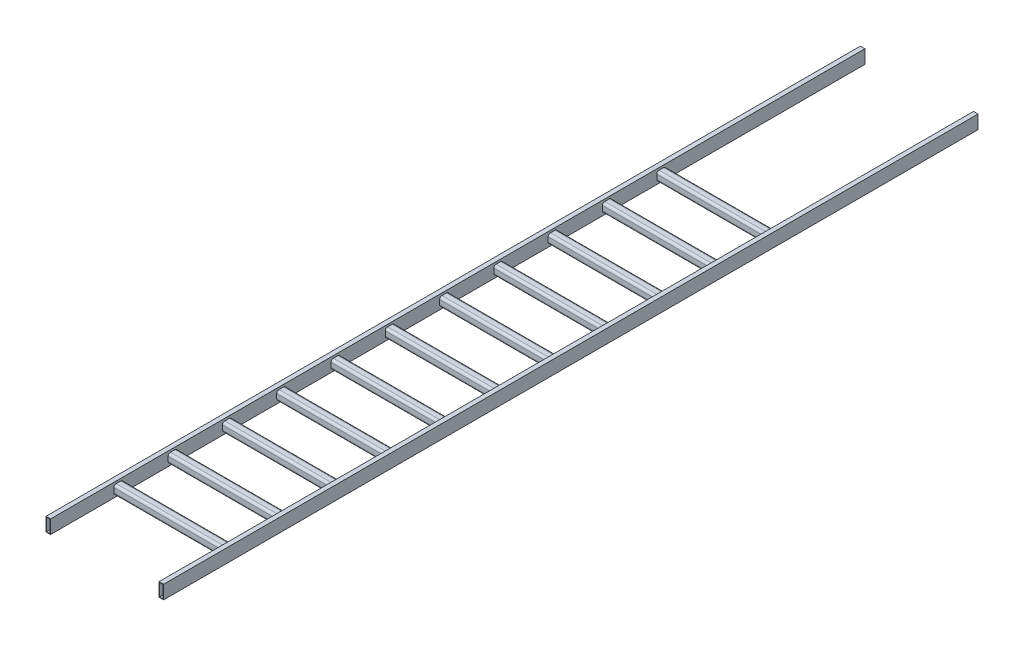
SolidWorks part; units mm, degrees
other "DetailItem3"
ref_plane "Front Plane" through (0, 0, 0) normal (0, 0, 1) x (1, 0, 0)
ref_plane "Top Plane" through (0, 0, 0) normal (0, 1, 0) x (1, 0, 0)
ref_plane "Right Plane" through (0, 0, 0) normal (1, 0, 0) x (0, 0, -1)
sketch "Sketch15" plane through (0, 0, 0) normal (0, 0, 1) x (1, 0, 0)
  line L0 (0, 222.2231) -> (0, -267.675) construction
  line L1 (-483.3871, 0) -> (603.0676, 0) construction
  line L2 (307.975, 34.925) -> (327.025, -34.925) construction
  line L3 (-304.8, -38.1) -> (-330.2, -38.1)
  line L4 (-304.8, -38.1) -> (-304.8, 38.1)
  line L5 (-304.8, 38.1) -> (-330.2, 38.1)
  line L6 (-330.2, -38.1) -> (-330.2, 38.1)
  line L7 (-304.8, -38.1) -> (-330.2, 38.1) construction
  line L8 (-304.8, 38.1) -> (-330.2, -38.1) construction
  line L9 (-307.975, -34.925) -> (-327.025, -34.925)
  line L10 (-307.975, -34.925) -> (-307.975, 34.925)
  line L11 (-307.975, 34.925) -> (-327.025, 34.925)
  line L12 (-327.025, -34.925) -> (-327.025, 34.925)
  line L13 (-307.975, -34.925) -> (-327.025, 34.925) construction
  line L14 (-307.975, 34.925) -> (-327.025, -34.925) construction
  line L15 (307.975, -34.925) -> (327.025, 34.925) construction
  line L16 (304.8, 38.1) -> (330.2, -38.1) construction
  line L17 (304.8, -38.1) -> (330.2, 38.1) construction
  line L18 (327.025, -34.925) -> (327.025, 34.925)
  line L19 (307.975, 34.925) -> (327.025, 34.925)
  line L20 (307.975, -34.925) -> (307.975, 34.925)
  line L21 (307.975, -34.925) -> (327.025, -34.925)
  line L22 (330.2, -38.1) -> (330.2, 38.1)
  line L23 (304.8, 38.1) -> (330.2, 38.1)
  line L24 (304.8, -38.1) -> (304.8, 38.1)
  line L25 (304.8, -38.1) -> (330.2, -38.1)
  point P3 (-317.5, 0)
  point P10 (-317.5, 0)
  point P24 (317.5, 0)
  dimension "D1" = 25.4
  dimension "D2" = 76.2
  dimension "D3" = 3.175
  dimension "D4" = 3.175
  dimension "D5" = 660.4
extrude "Boss-Extrude1" add sketch "Sketch15" along normal blind 4572
sketch "Sketch17" plane through (0, 0, 0) normal (0, 1, 0) x (1, 0, 0)
  line L0 (-304.8, -1143) -> (304.8, -1143)
  line L1 (-304.8, -4572) -> (-304.8, 0) construction
  line L2 (304.8, -4572) -> (304.8, 0) construction
  line L3 (330.2, 0) -> (304.8, 0) construction
  line L4 (-304.8, -1447.8) -> (304.8, -1447.8)
  line L5 (-304.8, -1752.6) -> (304.8, -1752.6)
  line L6 (-304.8, -2057.4) -> (304.8, -2057.4)
  line L7 (-304.8, -2362.2) -> (304.8, -2362.2)
  line L8 (-304.8, -2667) -> (304.8, -2667)
  line L9 (-304.8, -2971.8) -> (304.8, -2971.8)
  line L10 (-304.8, -3276.6) -> (304.8, -3276.6)
  line L11 (-304.8, -3581.4) -> (304.8, -3581.4)
  line L12 (-304.8, -3886.2) -> (304.8, -3886.2)
  line L13 (-304.8, -4191) -> (304.8, -4191)
  dimension "D1" = 1143
  dimension "D2" = 11
other "Square tube 2 X 2 X 0.25(3)"
ref_plane "Plane3" through (-304.8, 0, 1143) normal (1, 0, 0) x (0, 0, -1)
sketch "Sketch1" plane through (-304.8, 0, 1143) normal (1, 0, 0) x (0, 0, -1)
  line L0 (-12.7, -19.05) -> (12.7, -19.05)
  line L1 (-19.05, -12.7) -> (-19.05, 12.7)
  line L2 (12.7, 19.05) -> (-12.7, 19.05)
  line L3 (19.05, 12.7) -> (19.05, -12.7)
  line L4 (-12.7, -25.4) -> (12.7, -25.4)
  line L5 (-25.4, -12.7) -> (-25.4, 12.7)
  line L6 (12.7, 25.4) -> (-12.7, 25.4)
  line L7 (25.4, 12.7) -> (25.4, -12.7)
  line L8 (0, 0) -> (19.05, 0) construction
  line L9 (0, 0) -> (0, 19.05) construction
  arc A0 (25.4, 12.7) -> (12.7, 25.4) centre (12.7, 12.7) ccw
  arc A1 (12.7, -25.4) -> (25.4, -12.7) centre (12.7, -12.7) ccw
  arc A2 (-25.4, -12.7) -> (-12.7, -25.4) centre (-12.7, -12.7) ccw
  arc A3 (-12.7, 25.4) -> (-25.4, 12.7) centre (-12.7, 12.7) ccw
  arc A4 (-12.7, 19.05) -> (-19.05, 12.7) centre (-12.7, 12.7) ccw
  arc A5 (19.05, 12.7) -> (12.7, 19.05) centre (12.7, 12.7) ccw
  arc A6 (12.7, -19.05) -> (19.05, -12.7) centre (12.7, -12.7) ccw
  arc A7 (-19.05, -12.7) -> (-12.7, -19.05) centre (-12.7, -12.7) ccw
  point P3 (0, 25.4)
  point P4 (25.4, 0)
  point P5 (0, -25.4)
  point P6 (-25.4, 0)
  point P7 (-25.4, 25.4)
  point P8 (-25.4, -25.4)
  point P33 (0, 0)
  point P35 (25.4, -25.4)
  point P36 (25.4, 25.4)
  point P37 (0, 0)
  dimension "D1" = 12.7
  dimension "Thickness" = 6.35
  dimension "V_leg" = 50.8
sketch "Sketch114" plane through (-330.2, 0, 0) normal (-1, 0, 0) x (0, 0, 1)
  line L0 (4572, 38.1) -> (0, 38.1) construction
  line L1 (959.1398, 38.1) -> (1035.3398, 38.1)
  line L2 (959.1398, 38.1) -> (959.1398, -177.8)
  line L3 (959.1398, -177.8) -> (1035.3398, -177.8)
  line L4 (1035.3398, 38.1) -> (1035.3398, -177.8)
  dimension "D1" = 76.2
  dimension "D2" = 215.9
sketch "Sketch115" plane through (0, 0, 1117.6) normal (0, 0, -1) x (-1, 0, 0)
  line L0 (0, -251.514) -> (0, 249.2549) construction
  line L1 (-304.8, 12.7) -> (304.8, 12.7) construction
  line L2 (-101.6, -12.7) -> (-203.2, -12.7)
  line L3 (-101.6, -12.7) -> (-101.6, 12.7)
  line L4 (-101.6, 12.7) -> (-203.2, 12.7)
  line L5 (-203.2, -12.7) -> (-203.2, 12.7)
  line L6 (-101.6, -12.7) -> (-203.2, 12.7) construction
  line L7 (-101.6, 12.7) -> (-203.2, -12.7) construction
  line L8 (-304.8, -12.7) -> (304.8, -12.7) construction
  line L9 (101.6, 12.7) -> (203.2, -12.7) construction
  line L10 (101.6, -12.7) -> (203.2, 12.7) construction
  line L11 (203.2, -12.7) -> (203.2, 12.7)
  line L12 (101.6, 12.7) -> (203.2, 12.7)
  line L13 (101.6, -12.7) -> (101.6, 12.7)
  line L14 (101.6, -12.7) -> (203.2, -12.7)
  point P3 (-152.4, 0)
  point P16 (152.4, 0)
  dimension "D1" = 101.6
  dimension "D2" = 152.4
  dimension "D3" = 25.4
extrude "Boss-Extrude2" add sketch "Sketch115" along normal blind 0.0025 separate body
sketch "Bend-Lines1" [suppressed] plane through (0, 0, 0) normal (0, 1, 0) x (1, 0, 0)
sketch "Bounding-Box1" [suppressed] plane through (0, 0, 0) normal (0, 1, 0) x (1, 0, 0)
